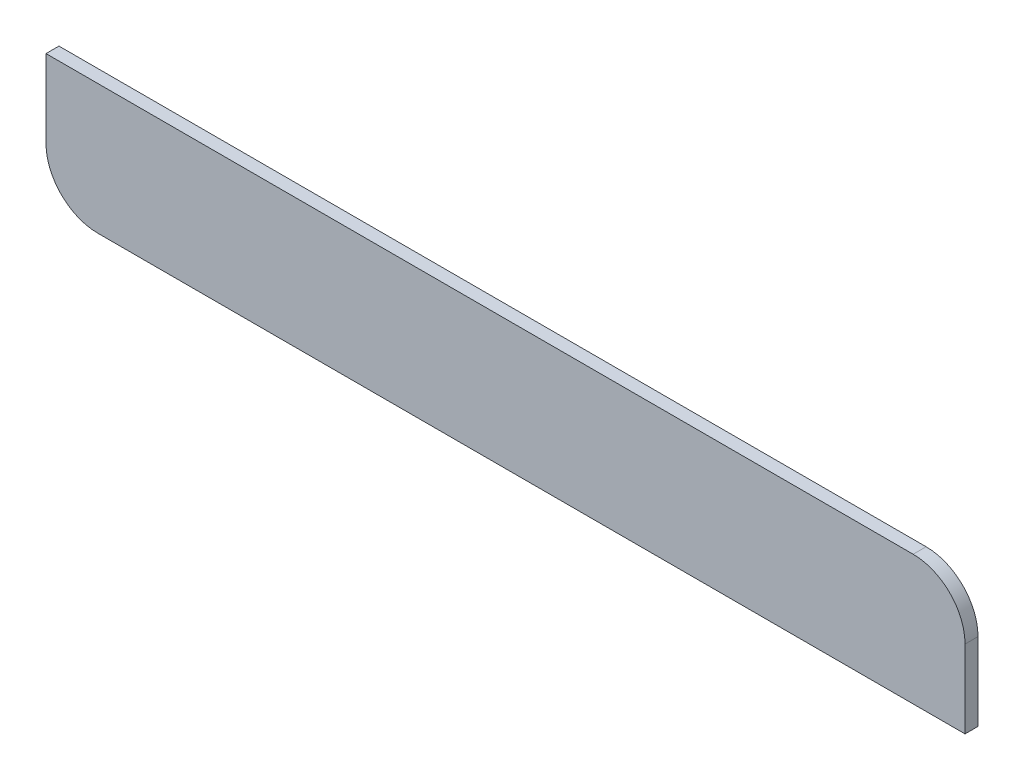
SolidWorks part; units mm, degrees
ref_plane "Front Plane" through (0, 0, 0) normal (0, 0, 1) x (1, 0, 0)
ref_plane "Top Plane" through (0, 0, 0) normal (0, 1, 0) x (1, 0, 0)
ref_plane "Right Plane" through (0, 0, 0) normal (1, 0, 0) x (0, 0, -1)
sketch "Sketch1" plane through (0, 0, 0) normal (0, 0, 1) x (1, 0, 0)
  line L1 (-60.6822, -10.1215) -> (363.9178, -10.1215)
  line L2 (-60.6822, -10.1215) -> (-60.6822, -48.2215)
  line L3 (-35.2822, -73.6215) -> (389.3178, -73.6215)
  line L4 (389.3178, -35.5215) -> (389.3178, -73.6215)
  arc A0 (389.3178, -35.5215) -> (363.9178, -10.1215) centre (363.9178, -35.5215) ccw
  arc A1 (-35.2822, -73.6215) -> (-60.6822, -48.2215) centre (-35.2822, -48.2215) cw
  point P6 (389.3178, -10.1215)
  point P9 (-60.6822, -73.6215)
  dimension "D3" = 25.4
  dimension "D1" = 450
  dimension "D2" = 63.5
extrude "Boss-Extrude1" add sketch "Sketch1" along normal blind 6.35
